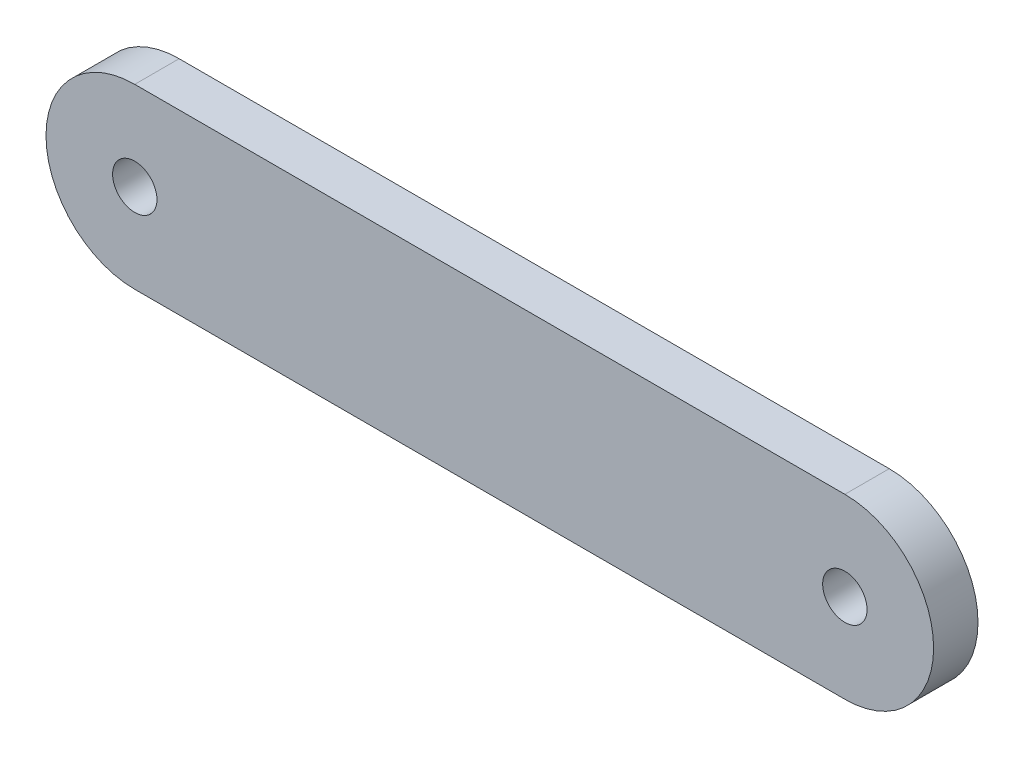
SolidWorks part; units mm, degrees
ref_plane "Front Plane" through (0, 0, 0) normal (0, 0, 1) x (1, 0, 0)
ref_plane "Top Plane" through (0, 0, 0) normal (0, 1, 0) x (1, 0, 0)
ref_plane "Right Plane" through (0, 0, 0) normal (1, 0, 0) x (0, 0, -1)
sketch "Sketch1" plane through (0, 0, 0) normal (0, 0, 1) x (1, 0, 0)
  line L1 (-48.768, 26.416) -> (2.032, 26.416)
  line L3 (-48.768, 13.716) -> (2.032, 13.716)
  arc A0 (-48.768, 26.416) -> (-48.768, 13.716) centre (-48.768, 20.066) ccw
  arc A1 (2.032, 13.716) -> (2.032, 26.416) centre (2.032, 20.066) ccw
  circle A2 centre (-48.768, 20.066) radius 1.5875
  circle A3 centre (2.032, 20.066) radius 1.5875
  dimension "D3" = 3.175
  dimension "D1" = 12.7
  dimension "D2" = 50.8
extrude "Boss-Extrude1" add sketch "Sketch1" along normal blind 3.175
